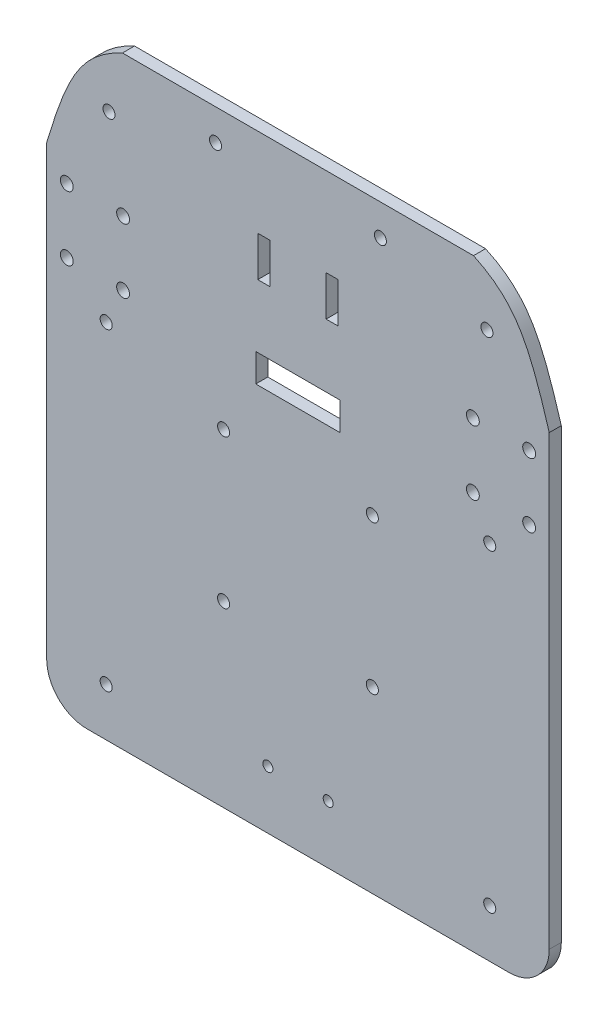
SolidWorks part; units mm, degrees
ref_plane "Front Plane" through (0, 0, 0) normal (0, 0, 1) x (1, 0, 0)
ref_plane "Top Plane" through (0, 0, 0) normal (0, 1, 0) x (1, 0, 0)
ref_plane "Right Plane" through (0, 0, 0) normal (1, 0, 0) x (0, 0, -1)
sketch "Sketch1" plane through (0, 0, 0) normal (0, 0, 1) x (1, 0, 0)
  line L1 (0, 0) -> (125, 0)
  line L2 (0, 0) -> (0, 150)
  line L3 (0, 150) -> (125, 150)
  line L4 (125, 0) -> (125, 150)
  dimension "D1" = 125
  dimension "D2" = 150
extrude "Boss-Extrude1" add sketch "Sketch1" along normal blind 3
sketch "Sketch2" plane through (0, 0, 0) normal (0, 0, -1) x (-1, 0, 0)
  line L2 (-120, 98.9581) -> (-106, 98.9581)
  line L3 (-120, 98.9581) -> (-120, 114.9581)
  line L4 (-120, 114.9581) -> (-106, 114.9581)
  line L5 (-106, 98.9581) -> (-106, 114.9581)
  line L6 (-120, 98.9581) -> (-106, 114.9581) construction
  line L7 (-120, 114.9581) -> (-106, 98.9581) construction
  line L8 (-19, 98.9581) -> (-5, 98.9581)
  line L9 (-19, 98.9581) -> (-19, 114.9581)
  line L10 (-19, 114.9581) -> (-5, 114.9581)
  line L11 (-5, 98.9581) -> (-5, 114.9581)
  line L12 (-19, 98.9581) -> (-5, 114.9581) construction
  line L13 (-19, 114.9581) -> (-5, 98.9581) construction
  line L14 (-125, 0) -> (-125, 150) construction
  line L15 (0, 150) -> (0, 0) construction
  circle A0 centre (-113, 106.9581) radius 5
  circle A1 centre (-120, 114.9581) radius 1.6
  circle A2 centre (-106, 114.9581) radius 1.6
  circle A3 centre (-106, 98.9581) radius 1.6
  circle A4 centre (-120, 98.9581) radius 1.6
  circle A5 centre (-12, 106.9581) radius 5
  circle A6 centre (-19, 114.9581) radius 1.6
  circle A7 centre (-5, 114.9581) radius 1.6
  circle A8 centre (-5, 98.9581) radius 1.6
  circle A9 centre (-19, 98.9581) radius 1.6
  dimension "D1" = 10
  dimension "D4" = 3.2
  dimension "D5" = 10
  dimension "D2" = 16
  dimension "D3" = 14
  dimension "D6" = 16
  dimension "D7" = 14
  dimension "D8" = 5
  dimension "D9" = 5
extrude "Cut-Extrude1" cut sketch "Sketch2" against normal through all contours A1 | A4 | A2 | A3 | A6 | A7 | A8 | A9
sketch "Sketch3" plane through (0, 0, 0) normal (0, 0, -1) x (-1, 0, 0)
  line L0 (0, 0) -> (-125, 0) construction
  line L1 (-81, 44.5) -> (-44, 44.5)
  line L2 (-81, 44.5) -> (-81, 81.5)
  line L3 (-81, 81.5) -> (-44, 81.5)
  line L4 (-44, 44.5) -> (-44, 81.5)
  line L5 (-81, 44.5) -> (-44, 81.5) construction
  line L6 (-81, 81.5) -> (-44, 44.5) construction
  line L7 (-125, 150) -> (0, 150) construction
  circle A0 centre (-81, 81.5) radius 1.5
  circle A1 centre (-44, 81.5) radius 1.5
  circle A2 centre (-81, 44.5) radius 1.5
  circle A3 centre (-44, 44.5) radius 1.5
  point P0 (-62.5, 63)
  point P12 (-62.5, 0)
  dimension "D1" = 3
  dimension "D2" = 37
  dimension "D3" = 87
extrude "Cut-Extrude2" cut sketch "Sketch3" against normal through all contours L3 A0 L2 | A1 | A2 | A3
sketch "Sketch4" plane through (0, 0, 0) normal (0, 0, -1) x (-1, 0, 0)
  line L0 (-62.5, 150) -> (-62.5, 0) construction
  line L1 (-125, 150) -> (0, 150) construction
  line L2 (0, 0) -> (-125, 0) construction
  line L3 (-69.9825, 14.4375) -> (-55.0175, 14.4375)
  circle A0 centre (-70.0175, 14.4375) radius 1.25
  circle A1 centre (-55.0175, 14.4375) radius 1.25
  point P15 (-62.5, 14.4375)
  dimension "D1" = 2.5
  dimension "D2" = 15
extrude "Cut-Extrude3" cut sketch "Sketch4" against normal through all contours A0 | A1
sketch "Sketch5" plane through (0, 0, 0) normal (0, 0, -1) x (-1, 0, 0)
  line L0 (-62.5, 150) -> (-62.5, 0) construction
  line L1 (-125, 150) -> (0, 150) construction
  line L2 (0, 0) -> (-125, 0) construction
  line L3 (-55.5, 128.0043) -> (-55.5, 118.0043)
  line L4 (-72.5, 128.0043) -> (-69.5, 128.0043)
  line L5 (-72.5, 128.0043) -> (-72.5, 118.0043)
  line L6 (-72.5, 118.0043) -> (-69.5, 118.0043)
  line L7 (-69.5, 128.0043) -> (-69.5, 118.0043)
  line L8 (-52.5, 118.0043) -> (-55.5, 118.0043)
  line L9 (-52.5, 128.0043) -> (-52.5, 118.0043)
  line L10 (-52.5, 128.0043) -> (-55.5, 128.0043)
  dimension "D1" = 3
  dimension "D2" = 10
  dimension "D3" = 7
extrude "Cut-Extrude4" cut sketch "Sketch5" against normal through all
sketch "Sketch6" plane through (0, 0, 0) normal (0, 0, -1) x (-1, 0, 0)
  line L0 (-62.5, 150) -> (-62.5, 0) construction
  line L1 (-125, 150) -> (0, 150) construction
  line L2 (0, 0) -> (-125, 0) construction
  circle A0 centre (-15.5, 135.6782) radius 1.5
  circle A1 centre (-109.5, 135.6782) radius 1.5
  dimension "D1" = 3
  dimension "D2" = 47
extrude "Cut-Extrude5" cut sketch "Sketch6" against normal through all
sketch "Sketch7" plane through (0, 0, 3) normal (0, 0, 1) x (1, 0, 0)
  line L0 (0, 150) -> (0, 0) construction
  line L1 (0, 121.3038) -> (5.1307, 138.5541) construction
  line L2 (5.1307, 138.5541) -> (8.0571, 143.1747) construction
  line L3 (8.0571, 143.1747) -> (13.2938, 147.4873) construction
  line L4 (13.2938, 147.4873) -> (18.8386, 150) construction
  line L5 (125, 150) -> (0, 150) construction
  line L6 (18.8386, 150) -> (0, 150)
  line L7 (0, 150) -> (0, 121.3038)
  line L8 (62.5, 150) -> (62.5, 0) construction
  line L9 (0, 0) -> (125, 0) construction
  line L10 (125, 121.3038) -> (119.8693, 138.5541) construction
  line L11 (119.8693, 138.5541) -> (116.9429, 143.1747) construction
  line L12 (116.9429, 143.1747) -> (111.7062, 147.4873) construction
  line L13 (111.7062, 147.4873) -> (106.1614, 150) construction
  line L14 (125, 150) -> (125, 121.3038)
  line L15 (106.1614, 150) -> (125, 150)
  spline S0 degree 4 poles (0, 121.3038) (5.1307, 138.5541) (8.0571, 143.1747) (13.2938, 147.4873) (18.8386, 150) knots 0 0 0 0 0 1 1 1 1 1
  spline S1 degree 4 poles (125, 121.3038) (119.8693, 138.5541) (116.9429, 143.1747) (111.7062, 147.4873) (106.1614, 150) knots 0 0 0 0 0 1 1 1 1 1
extrude "Cut-Extrude6" cut sketch "Sketch7" against normal through all
sketch "Sketch8" plane through (0, 0, 3) normal (0, 0, 1) x (1, 0, 0)
  line L0 (62.5, 150) -> (62.5, 0) construction
  line L1 (106.1614, 150) -> (18.8386, 150) construction
  line L2 (0, 0) -> (125, 0) construction
  circle A0 centre (14.8, 12) radius 1.5
  circle A1 centre (110.2, 12) radius 1.5
  circle A2 centre (14.8, 90) radius 1.5
  circle A3 centre (110.2, 90) radius 1.5
  dimension "D1" = 3
  dimension "D2" = 12
  dimension "D3" = 47.7
  dimension "D4" = 78
extrude "Cut-Extrude7" cut sketch "Sketch8" against normal through all
sketch "Sketch9" plane through (0, 0, 3) normal (0, 0, 1) x (1, 0, 0)
  line L0 (62.5, 150) -> (62.5, 0) construction
  line L1 (106.1614, 150) -> (18.8386, 150) construction
  line L2 (0, 0) -> (125, 0) construction
  circle A0 centre (42, 142.2272) radius 1.5
  circle A1 centre (83, 142.2272) radius 1.5
  dimension "D1" = 3
  dimension "D2" = 20.5
extrude "Cut-Extrude8" cut sketch "Sketch9" against normal through all
fillet "Fillet3" radius 10 2 edges at (125, 0, 1.5) (0, 0, 1.5)
sketch "Sketch10" plane through (0, 0, 3) normal (0, 0, 1) x (1, 0, 0)
  line L0 (106.1614, 150) -> (18.8386, 150) construction
  line L1 (52, 102.2831) -> (73, 102.2831)
  line L2 (52, 102.2831) -> (52, 95.2831)
  line L3 (52, 95.2831) -> (73, 95.2831)
  line L4 (73, 102.2831) -> (73, 95.2831)
  point P4 (62.5, 102.2831)
  point P7 (62.5, 150)
  dimension "D1" = 7
  dimension "D2" = 21
extrude "Cut-Extrude9" cut sketch "Sketch10" against normal through all
